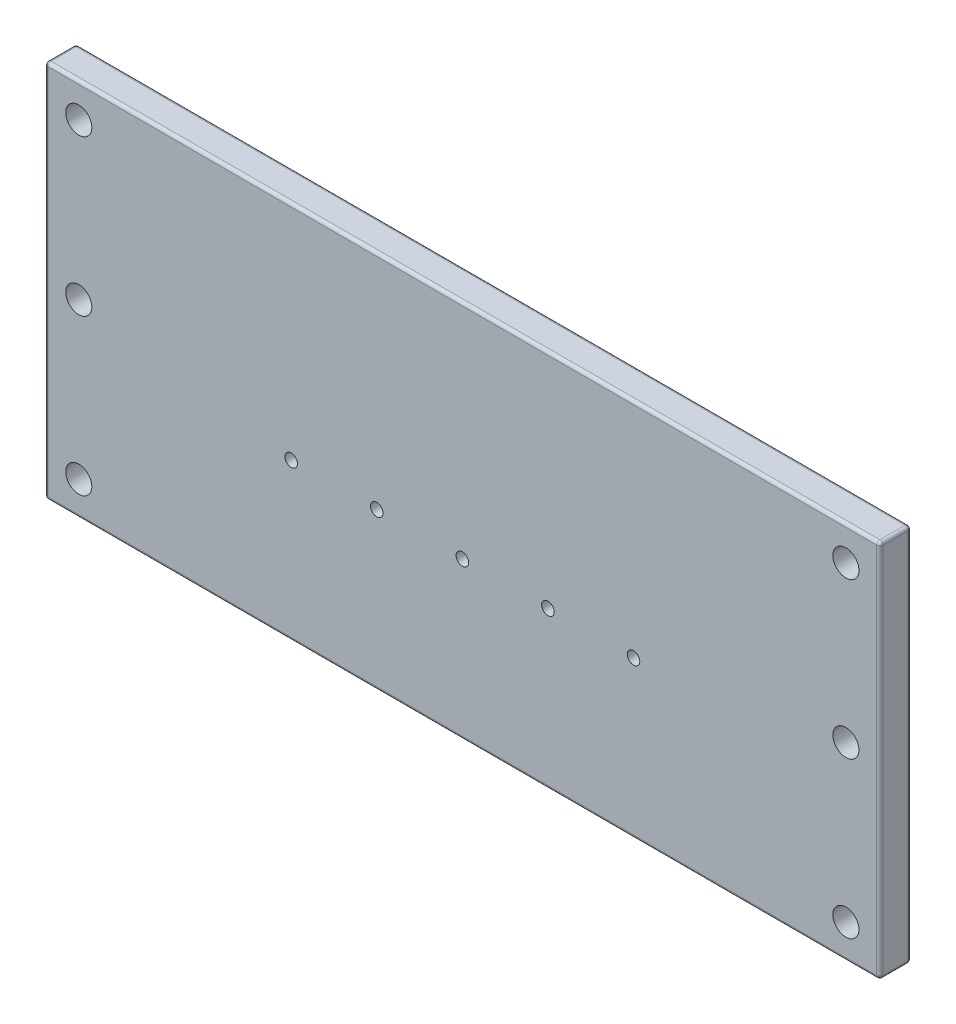
SolidWorks part; units mm, degrees
ref_plane "Front Plane" through (0, 0, 0) normal (0, 0, 1) x (1, 0, 0)
ref_plane "Top Plane" through (0, 0, 0) normal (0, 1, 0) x (1, 0, 0)
ref_plane "Right Plane" through (0, 0, 0) normal (1, 0, 0) x (0, 0, -1)
sketch "Sketch1" plane through (0, 0, 0) normal (0, 0, 1) x (1, 0, 0)
  line L1 (0, 0) -> (800, 0)
  line L2 (0, 0) -> (0, 363)
  line L3 (0, 363) -> (800, 363)
  line L4 (800, 0) -> (800, 363)
  dimension "D1" = 800
  dimension "D2" = 363
extrude "Boss-Extrude1" add sketch "Sketch1" along normal blind 30
sketch "Sketch2" plane through (0, 0, 30) normal (0, 0, 1) x (1, 0, 0)
  line L0 (0, 0) -> (800, 0) construction
  line L1 (0, 363) -> (0, 0) construction
  circle A0 centre (32.5, 32.5) radius 12.5
  dimension "D1" = 25
  dimension "D2" = 32.5
  dimension "D3" = 32.5
extrude "Cut-Extrude1" cut sketch "Sketch2" against normal blind 30
pattern_linear "LPattern1" count 3 spacing 149 along (0, 1, 0) count 2 spacing 735 along (1, 0, 0) of "Cut-Extrude1"
sketch "Sketch3" plane through (0, 0, 30) normal (0, 0, 1) x (1, 0, 0)
  line L0 (0, 0) -> (800, 0) construction
  line L1 (0, 363) -> (0, 0) construction
  circle A0 centre (236, 150) radius 6
  dimension "D1" = 12
  dimension "D2" = 150
  dimension "D3" = 236
extrude "Cut-Extrude2" cut sketch "Sketch3" against normal blind 20
pattern_linear "LPattern2" count 5 spacing 82 along (1, 0, 0) of "Cut-Extrude2"
sketch "Sketch4" plane through (0, 0, 0) normal (0, -1, 0) x (1, 0, 0)
  line L0 (0, 0) -> (800, 0) construction
  line L1 (0, 30) -> (0, 0) construction
  circle A0 centre (92.53, 10) radius 5
  dimension "D1" = 10
  dimension "D2" = 10
  dimension "D3" = 92.53
extrude "Cut-Extrude3" cut sketch "Sketch4" against normal blind 18
pattern_linear "LPattern3" count 10 spacing 68.33 along (1, 0, 0) of "Cut-Extrude3"
fillet "Fillet1" radius 3 12 edges at (0, 181.5, 30) (0, 181.5, 0) (400, 0, 30) (400, 0, 0) (800, 181.5, 30) (800, 181.5, 0) (400, 363, 30) (400, 363, 0) (0, 363, 15) (0, 0, 15) (800, 363, 15) (800, 0, 15)
